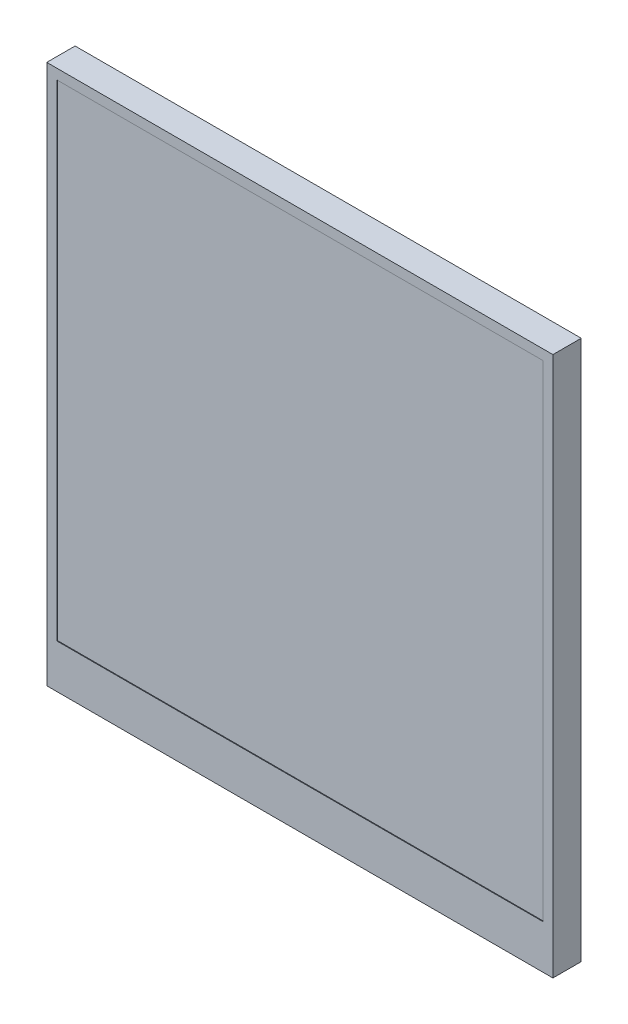
SolidWorks part; units mm, degrees
ref_plane "Front Plane" through (0, 0, 0) normal (0, 0, 1) x (1, 0, 0)
ref_plane "Top Plane" through (0, 0, 0) normal (0, 1, 0) x (1, 0, 0)
ref_plane "Right Plane" through (0, 0, 0) normal (1, 0, 0) x (0, 0, -1)
sketch "Sketch1" plane through (0, 0, 0) normal (0, 0, 1) x (1, 0, 0)
  line L1 (0, 0) -> (75, 0)
  line L2 (0, 0) -> (0, 80)
  line L3 (0, 80) -> (75, 80)
  line L4 (75, 0) -> (75, 80)
  dimension "D1" = 80
  dimension "D2" = 75
extrude "Boss-Extrude1" add sketch "Sketch1" along normal blind 4.2
sketch "Sketch2" plane through (0, 0, 4.2) normal (0, 0, 1) x (1, 0, 0)
  line L0 (75, 80) -> (0, 80) construction
  line L1 (1.5, 78.5) -> (73.5, 78.5)
  line L2 (1.5, 78.5) -> (1.5, 6.5)
  line L3 (1.5, 6.5) -> (73.5, 6.5)
  line L4 (73.5, 78.5) -> (73.5, 6.5)
  point P6 (37.5, 80)
  dimension "D1" = 72
  dimension "D2" = 72
  dimension "D3" = 36
  dimension "D4" = 1.5
extrude "Cut-Extrude1" cut sketch "Sketch2" against normal blind 0.1
sketch "Sketch3" plane through (0, 0, 0) normal (0, 0, -1) x (-1, 0, 0)
  line L0 (0, 80) -> (0, 0) construction
  line L1 (-75, 80) -> (0, 80) construction
  circle A0 centre (-3.5, 75) radius 1.35
  circle A1 centre (-61.5, 75) radius 1.35
  circle A2 centre (-3.5, 26) radius 1.35
  circle A3 centre (-61.5, 26) radius 1.35
  circle A4 centre (-61.5, 75) radius 3
  circle A5 centre (-3.5, 75) radius 3
  circle A6 centre (-3.5, 26) radius 3
  circle A7 centre (-61.5, 26) radius 3
  dimension "D2" = 2.7
  dimension "D3" = 2.7
  dimension "D5" = 2.7
  dimension "D7" = 2.7
  dimension "D9" = 6
  dimension "D11" = 6
  dimension "D12" = 6
  dimension "D13" = 6
  dimension "D1" = 3.5
  dimension "D4" = 58
  dimension "D6" = 49
  dimension "D8" = 58
  dimension "D10" = 5
extrude "Boss-Extrude2" add sketch "Sketch3" along normal blind 2
